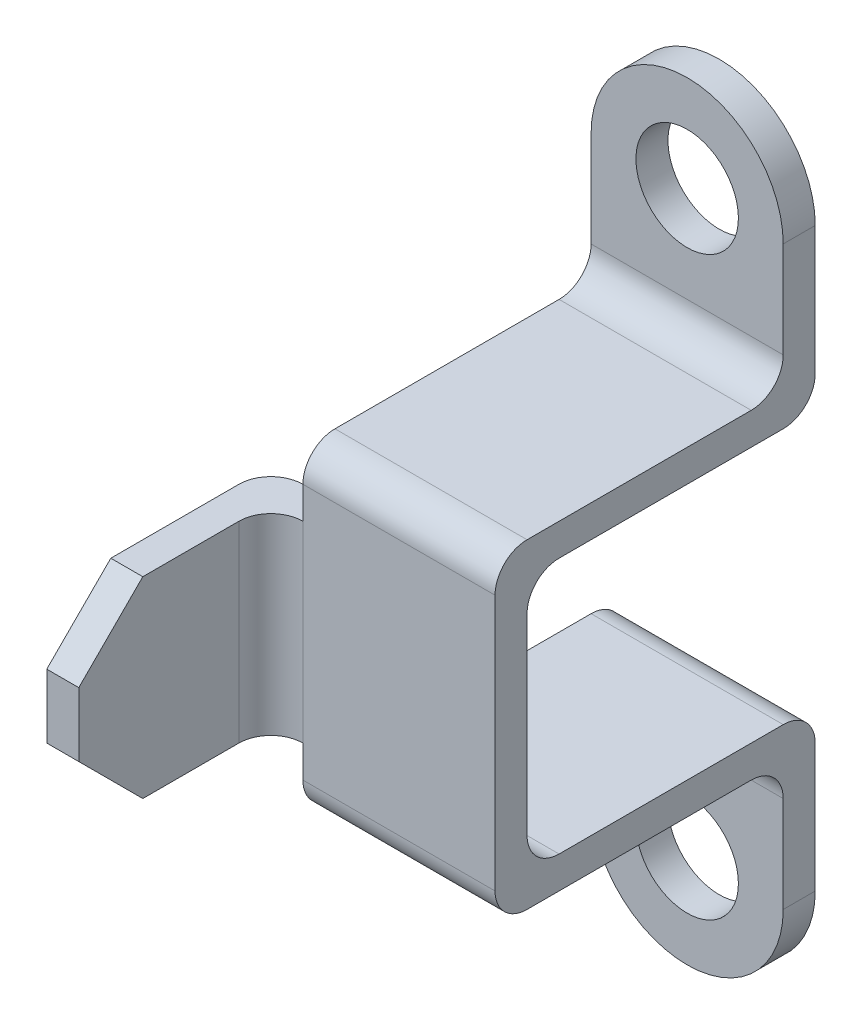
SolidWorks part; units mm, degrees
material "Plain Carbon Steel"
ref_plane "Front Plane" through (0, 0, 0) normal (1, 0, 0) x (0, 1, 0)
ref_plane "Top Plane" through (0, 0, 0) normal (0, 0, 1) x (0, 1, 0)
ref_plane "Right Plane" through (0, 0, 0) normal (0, 1, 0) x (-1, 0, 0)
sketch "Sketch1" plane through (0, 0, 0) normal (1, 0, 0) x (0, 1, 0)
  line L0 (45, 0) -> (45, 5)
  line L1 (45, 5) -> (25, 5)
  line L2 (25, 5) -> (25, 50)
  line L3 (25, 50) -> (0, 50)
  line L4 (0, 50) -> (0, 45)
  line L5 (0, 45) -> (20, 45)
  line L6 (20, 45) -> (20, 0)
  line L7 (20, 0) -> (45, 0)
  dimension "D1" = 50
  dimension "D2" = 20
  dimension "D3" = 5
  dimension "D4" = 5
  dimension "D5" = 5
  dimension "D6" = 45
extrude "Boss-Extrude1" add sketch "Sketch1" along normal mid plane 30
fillet "Fillet1" radius 5 1 edges at (0, 25, 5)
fillet "Fillet2" radius 5 3 edges at (0, 20, 45) (0, 25, 50) (0, 20, 0)
sketch "Sketch4" plane through (0, 0, 0) normal (0, 1, 0) x (-1, 0, 0)
  line L1 (15, 50) -> (20, 50)
  line L2 (15, 50) -> (15, 45)
  line L3 (15, 45) -> (20, 45)
  line L4 (20, 50) -> (20, 45)
  dimension "D1" = 5
  dimension "D2" = 5
extrude "Boss-Extrude2" add sketch "Sketch4" along normal blind 15
sketch "Sketch6" plane through (-20, 0, 0) normal (-1, 0, 0) x (0, -1, 0)
  line L1 (0, 45) -> (-15, 45)
  line L2 (0, 45) -> (0, 80)
  line L3 (0, 80) -> (-15, 80)
  line L4 (-15, 45) -> (-15, 80)
  dimension "D1" = 15
  dimension "D2" = 35
extrude "Boss-Extrude3" add sketch "Sketch6" along normal blind 5
fillet "Fillet3" radius 5 2 edges at (-25, 7.5, 45) (-20, 7.5, 50)
chamfer "Chamfer1" distance 10 angle 45 1 edges at (-22.5, 15, 80)
sketch "Sketch8" plane through (0, 0, 5) normal (0, 0, 1) x (1, 0, 0)
  line L1 (-15, 45) -> (15, 45)
  line L2 (15, 45) -> (15, 30) construction
  arc A0 (-15, 45) -> (15, 45) centre (0, 45) cw
  point P0 (0, 60)
  dimension "D1" = 15
  dimension "D2" = 30
  dimension "D3" = 60
extrude "Boss-Extrude4" add sketch "Sketch8" against normal blind 5
sketch "Sketch9" plane through (0, 0, 5) normal (0, 0, 1) x (1, 0, 0)
  circle A0 centre (0, 45) radius 8
  arc A1 (15, 45) -> (-15, 45) centre (0, 45) ccw construction
  dimension "D1" = 16
extrude "Cut-Extrude6" cut sketch "Sketch9" against normal blind 5
mirror "Mirror2" about plane through (15, 0, 50) normal (0, 1, 0) of bodies 105
